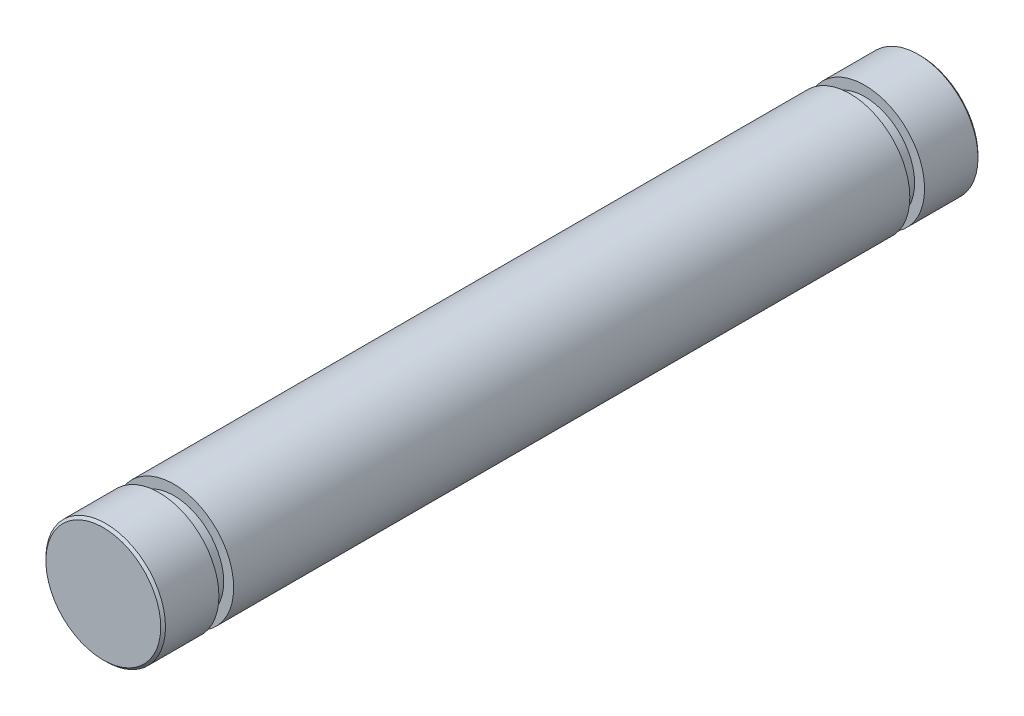
SolidWorks part; units mm, degrees
ref_plane "Front Plane" through (0, 0, 0) normal (0, 0, 1) x (1, 0, 0)
ref_plane "Top Plane" through (0, 0, 0) normal (0, 1, 0) x (1, 0, 0)
ref_plane "Right Plane" through (0, 0, 0) normal (1, 0, 0) x (0, 0, -1)
sketch "Sketch1" plane through (0, 0, 0) normal (1, 0, 0) x (0, 0, -1)
  line L0 (-20.5, 0) -> (20.5, 0) construction
  line L1 (0, -3) -> (0, 3) construction
  point P4 (0, 0)
  point P8 (0, 0)
sketch "Sketch2" plane through (0, 0, 0) normal (0, 0, 1) x (1, 0, 0)
  circle A0 centre (0, 0) radius 3
extrude "Boss-Extrude1" add sketch "Sketch2" along normal up to vertex (20.5 mm away) and the other way up to vertex (20.5 mm away) up to point (0, 0, 20.5) other way up to point (0, 0, -20.5)
chamfer "Chamfer1" distance 0.12 angle 45 2 edges at (3, 0, -20.5) (3, 0, 20.5)
ref_plane "Plane1" through (0, 0, 19.8) normal (0, 0, 1) x (1, 0, 0)
sketch "Sketch3" plane through (0, 0, 19.8) normal (0, 0, 1) x (1, 0, 0)
  circle A0 centre (0, 0) radius 3 construction
  circle A1 centre (0, 0) radius 3
  circle A2 centre (0, 0) radius 2.5
  dimension "D1" = 0.5
extrude "Cut-Extrude1" cut sketch "Sketch3" against normal blind 0.74 from offset 2.1 offset against normal yes
mirror "Mirror1" about plane through (0, 0, 0) normal (0, 0, 1) of "Cut-Extrude1"
equation "\"D1@Chamfer1\"=\"Diameter@Sketch1\"*.02"
